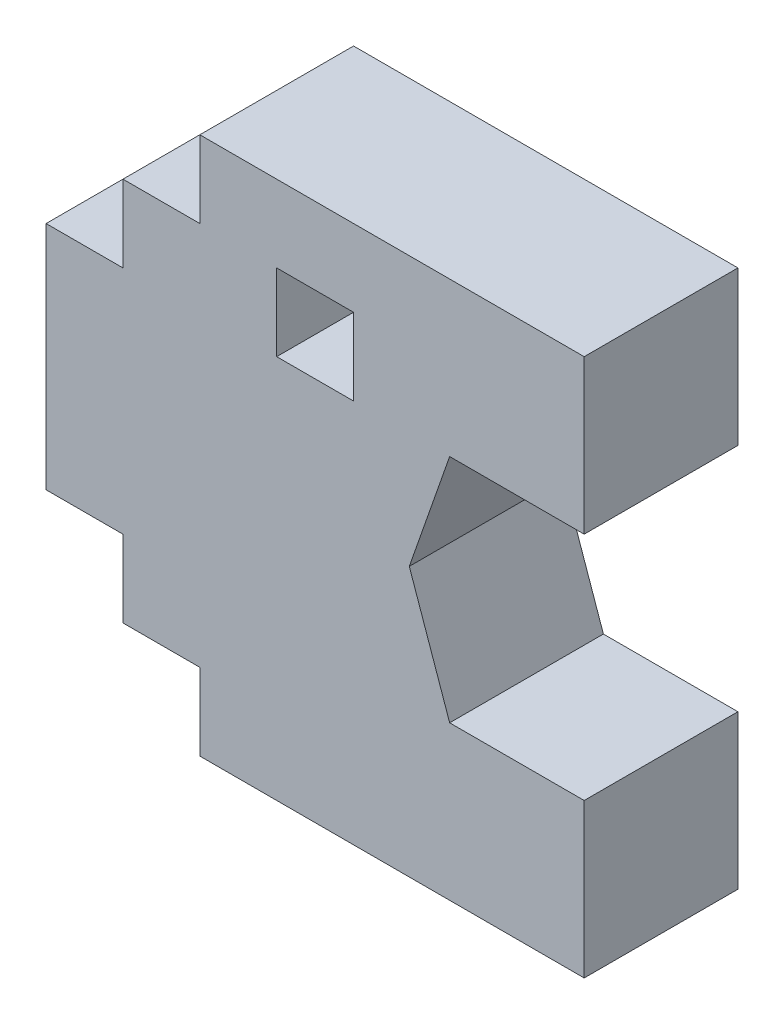
SolidWorks part; units mm, degrees
ref_plane "Front" through (0, 0, 0) normal (0, 0, 1) x (1, 0, 0)
ref_plane "Top" through (0, 0, 0) normal (0, 1, 0) x (1, 0, 0)
ref_plane "Right" through (0, 0, 0) normal (1, 0, 0) x (0, 0, -1)
sketch "Sketch1" plane through (0, 0, 0) normal (0, 0, 1) x (1, 0, 0)
  line L0 (0, 0) -> (100, 0)
  line L1 (100, 0) -> (100, 40)
  line L2 (100, 40) -> (65, 40)
  line L3 (65, 40) -> (54.5, 70)
  line L4 (40, 120) -> (40, 100)
  line L5 (0, 120) -> (0, 140)
  line L6 (-20, 120) -> (0, 120)
  line L7 (-40, 100) -> (-40, 40)
  line L8 (-40, 40) -> (-20, 40)
  line L9 (-20, 40) -> (-20, 20)
  line L10 (-20, 20) -> (0, 20)
  line L11 (0, 20) -> (0, 0)
  line L12 (-20, 100) -> (-20, 120)
  line L13 (-40, 100) -> (-20, 100)
  line L14 (65, 100) -> (54.5, 70)
  line L15 (100, 100) -> (65, 100)
  line L16 (100, 140) -> (100, 100)
  line L17 (0, 140) -> (100, 140)
  line L18 (20, 120) -> (20, 100)
  line L19 (20, 120) -> (40, 120)
  line L20 (20, 100) -> (40, 100)
  line L21 (65, 100) -> (100, 100)
  line L22 (0, 100) -> (100, 100) construction
  line L23 (0, 120) -> (100, 120) construction
  line L24 (40, 140) -> (40, 100) construction
  line L25 (20, 140) -> (20, 100) construction
  dimension "D1" = 100
  dimension "D2" = 20
  dimension "D3" = 20
  dimension "D5" = 20
  dimension "D6" = 20
  dimension "D9" = 40
  dimension "D10" = 35
extrude "Extrude1" add sketch "Sketch1" along normal blind 40 contours L17 L5 L6 L12 L13 L7 L8 L9 L10 L11 L0 L1 L2 L3 L14 L15 L16 L20 L18 L19 L4
